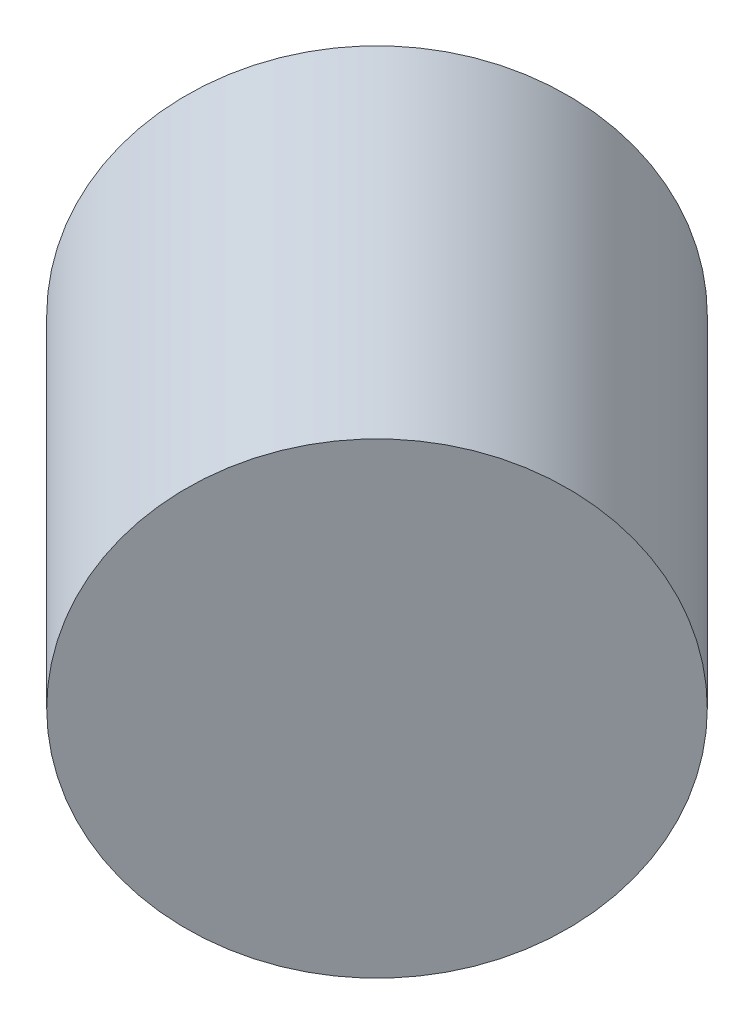
SolidWorks part; units mm, degrees
ref_plane "Front Plane" through (0, 0, 0) normal (0, 0, 1) x (1, 0, 0)
ref_plane "Top Plane" through (0, 0, 0) normal (0, 1, 0) x (1, 0, 0)
ref_plane "Right Plane" through (0, 0, 0) normal (1, 0, 0) x (0, 0, -1)
ref_plane "Plane1" through (-79.2786, 0, -79.2786) normal (0.7071, 0, 0.7071) x (0.7071, 0, -0.7071)
sketch "Sketch1" plane through (-79.2786, 0, -79.2786) normal (0.7071, 0, 0.7071) x (0.7071, 0, -0.7071)
  circle B0 centre (-226.1678, -7.5) radius 49
sketch_block_instance "Block1-1"
sketch_block "Block1"
extrude "Boss-Extrude1" add sketch "Sketch1" against normal blind 101
